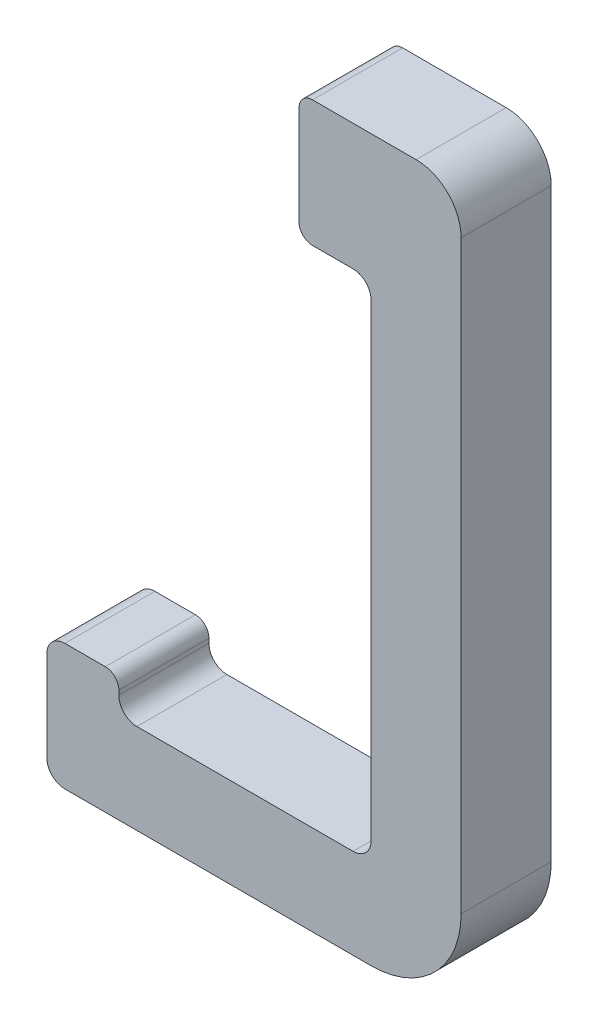
SolidWorks part; units mm, degrees
ref_plane "前视基准面" through (0, 0, 0) normal (0, 0, 1) x (1, 0, 0)
ref_plane "上视基准面" through (0, 0, 0) normal (0, 1, 0) x (1, 0, 0)
ref_plane "右视基准面" through (0, 0, 0) normal (1, 0, 0) x (0, 0, -1)
sketch "草图1" plane through (0, 0, 0) normal (0, 0, 1) x (1, 0, 0)
  line L1 (-6.5, 66) -> (-2, 66)
  line L2 (0, 64) -> (0, 16)
  line L4 (-36, 12) -> (-36, 2)
  line L5 (-34, 0) -> (0, 0)
  line L6 (10, 10) -> (10, 75)
  line L7 (5, 80) -> (-6.5, 80)
  line L9 (-8, 78.5) -> (-8, 67.5)
  line L10 (-28, 12.5) -> (-28, 12)
  line L11 (-26, 10) -> (-6.5, 10)
  line L13 (-29.5, 14) -> (-34, 14)
  line L14 (-6.5, 10) -> (-2, 10)
  line L15 (0, 12) -> (0, 16)
  arc A0 (-2, 66) -> (0, 64) centre (-2, 64) cw
  arc A1 (-6.5, 80) -> (-8, 78.5) centre (-6.5, 78.5) ccw
  arc A2 (-8, 67.5) -> (-6.5, 66) centre (-6.5, 67.5) ccw
  arc A4 (10, 75) -> (5, 80) centre (5, 75) ccw
  arc A5 (0, 0) -> (10, 10) centre (0, 10) ccw
  arc A6 (-36, 2) -> (-34, 0) centre (-34, 2) ccw
  arc A7 (-34, 14) -> (-36, 12) centre (-34, 12) ccw
  arc A8 (-28, 12) -> (-26, 10) centre (-26, 12) ccw
  arc A9 (-2, 10) -> (0, 12) centre (-2, 12) ccw
  arc A10 (-28, 12.5) -> (-29.5, 14) centre (-29.5, 12.5) ccw
  point P14 (-8, 80)
  point P17 (-8, 66)
  point P22 (10, 80)
  point P25 (10, 0)
  point P28 (-36, 0)
  dimension "D7" = 2
  dimension "D8" = 1.5
  dimension "D9" = 8
  dimension "D10" = 10
  dimension "D11" = 2
  dimension "D13" = 2
  dimension "D14" = 1.5
  dimension "D15" = 5
  dimension "D1" = 14
  dimension "D2" = 10
  dimension "D3" = 10
  dimension "D4" = 18
  dimension "D5" = 80
  dimension "D6" = 46
  dimension "D12" = 14
extrude "凸台-拉伸1" add sketch "草图1" along normal blind 10
